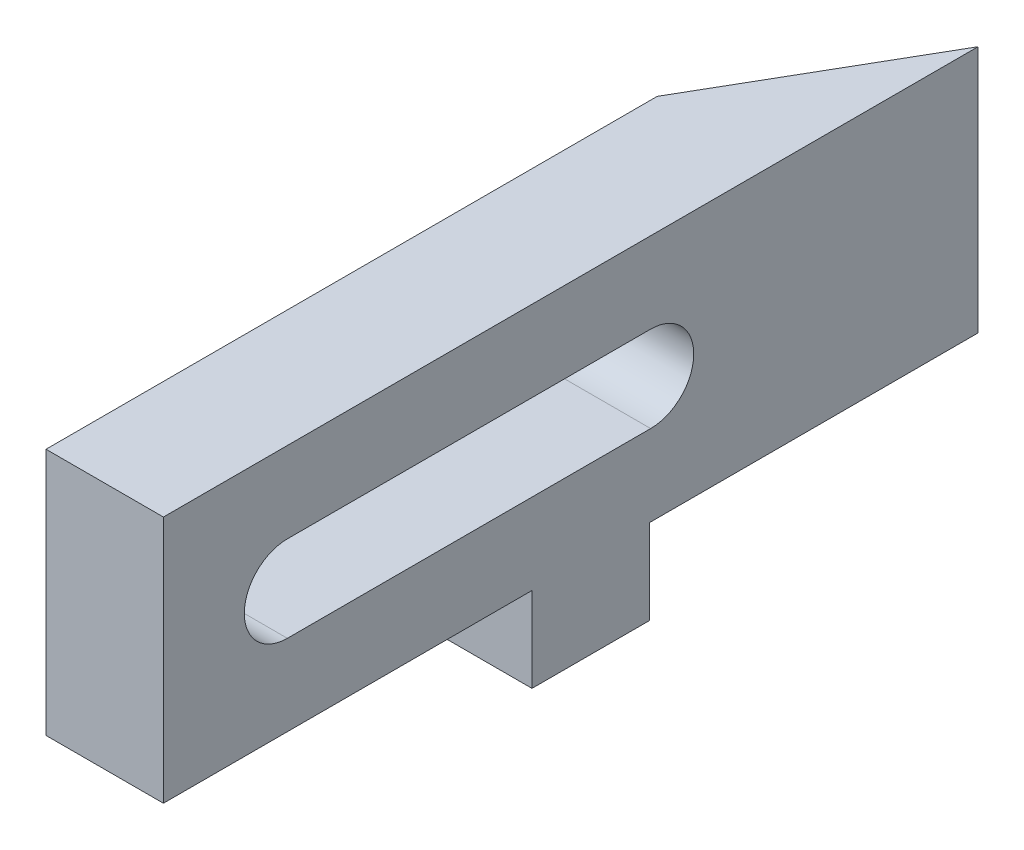
SolidWorks part; units mm, degrees
ref_plane "Front Plane" through (0, 0, 0) normal (0, 0, 1) x (1, 0, 0)
ref_plane "Top Plane" through (0, 0, 0) normal (0, 1, 0) x (1, 0, 0)
ref_plane "Right Plane" through (0, 0, 0) normal (1, 0, 0) x (0, 0, -1)
sketch "Sketch1" plane through (0, 0, 0) normal (0, 1, 0) x (1, 0, 0)
  line L0 (0, 0) -> (75, 0) construction
  line L1 (75, 0) -> (37.5, 64.9519) construction
  line L2 (37.5, 64.9519) -> (0, 0) construction
  line L3 (37.5, 64.9519) -> (37.5, 0) construction
  line L4 (15.5, 26.8468) -> (15.5, -20)
  line L5 (15.5, -20) -> (24.5, -20)
  line L6 (24.5, -20) -> (24.5, 42.4352)
  line L7 (24.5, 42.4352) -> (15.5, 26.8468)
  dimension "D1" = 75
  dimension "D2" = 75
  dimension "D3" = 75
  dimension "D4" = 13
  dimension "D5" = 9
  dimension "D6" = 20
extrude "Boss-Extrude1" add sketch "Sketch1" along normal blind 19
sketch "Sketch3" plane through (15.5, 0, 0) normal (-1, 0, 0) x (0, 0, 1)
  line L0 (-17.3468, 9.5) -> (10.5, 9.5) construction
  line L1 (-17.3468, 12.8) -> (10.5, 12.8)
  line L2 (-17.3468, 6.2) -> (10.5, 6.2)
  line L3 (-26.8468, 19) -> (20, 19) construction
  line L4 (-26.8468, 19) -> (-26.8468, 0) construction
  line L5 (20, 19) -> (20, 0) construction
  arc A0 (-17.3468, 12.8) -> (-17.3468, 6.2) centre (-17.3468, 9.5) ccw
  arc A1 (10.5, 6.2) -> (10.5, 12.8) centre (10.5, 9.5) ccw
  point P2 (-3.4234, 9.5)
  dimension "D4" = 3.3
  dimension "D1" = 9.5
  dimension "D2" = 9.5
  dimension "D3" = 9.5
extrude "Cut-Extrude1" cut sketch "Sketch3" against normal through all
sketch "Sketch4" plane through (0, 0, 0) normal (0, -1, 0) x (1, 0, 0)
  line L0 (15.5, -8.25) -> (24.5, -8.25)
  line L1 (15.5, -26.8468) -> (15.5, 20) construction
  line L2 (24.5, 20) -> (24.5, -42.4352) construction
  line L3 (24.5, -8.25) -> (24.5, -17.25)
  line L4 (24.5, -17.25) -> (15.5, -17.25)
  line L5 (15.5, -17.25) -> (15.5, -8.25)
  line L6 (15.5, 20) -> (24.5, 20) construction
  point P6 (20, 20)
  dimension "D1" = 9
  dimension "D2" = 28.25
extrude "Boss-Extrude2" add sketch "Sketch4" along normal blind 6.5
